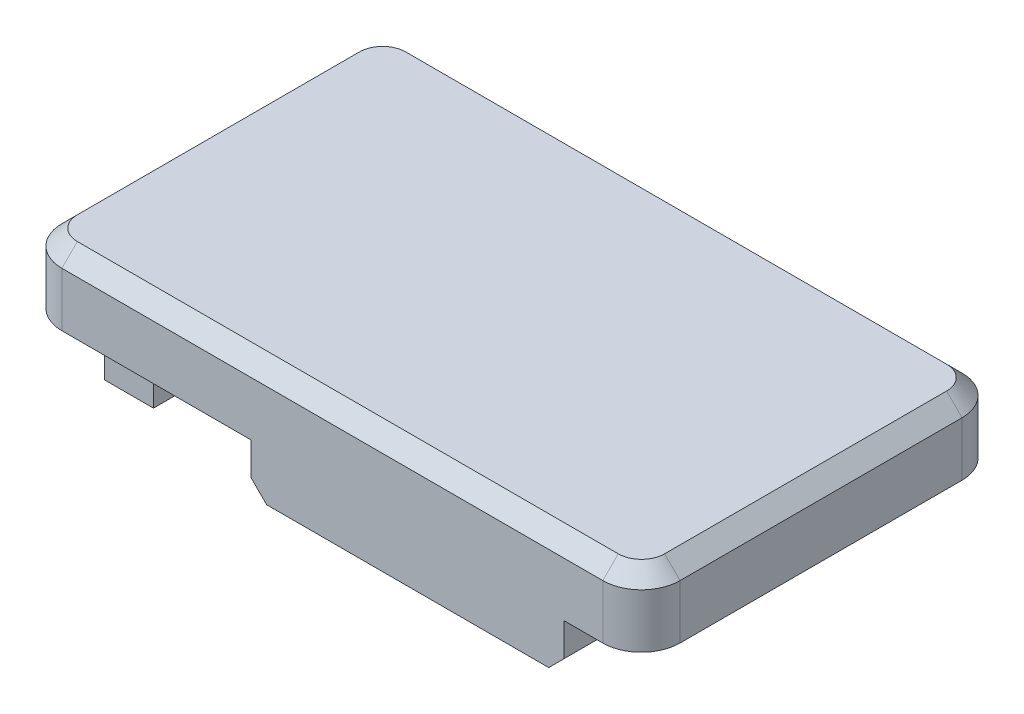
SolidWorks part; units mm, degrees
ref_plane "前视基准面" through (0, 0, 0) normal (0, 0, 1) x (1, 0, 0)
ref_plane "上视基准面" through (0, 0, 0) normal (0, 1, 0) x (1, 0, 0)
ref_plane "右视基准面" through (0, 0, 0) normal (1, 0, 0) x (0, 0, -1)
sketch "草图1" plane through (0, 0, 0) normal (0, 1, 0) x (1, 0, 0)
  line L0 (62.2995, 0) -> (94.2995, 0)
  line L1 (94.2995, 0) -> (94.2995, 18.6)
  line L2 (94.2995, 18.6) -> (62.2995, 18.6)
  line L3 (62.2995, 18.6) -> (62.2995, 0)
extrude "凸台-拉伸1" add sketch "草图1" along normal blind 3.6
sketch "草图2" plane through (0, 0, 0) normal (0, -1, 0) x (1, 0, 0)
  line L5 (64.2995, -2.2) -> (64.2995, -12.36)
  line L6 (64.2995, -12.36) -> (66.8395, -12.36)
  line L7 (66.8395, -12.36) -> (66.8395, -2.2)
  line L8 (66.8395, -2.2) -> (64.2995, -2.2)
extrude "凸台-拉伸2" add sketch "草图2" along normal blind 3.3
sketch "草图3" plane through (0, 0, 0) normal (0, -1, 0) x (1, 0, 0)
  line L1 (94.2995, -18.6) -> (62.2995, -18.6) construction
  line L2 (90.2995, -18.6) -> (74.0995, -18.6)
  line L3 (74.0995, -18.6) -> (74.0995, -16.6)
  line L4 (74.0995, -16.6) -> (90.2995, -16.6)
  line L5 (90.2995, -16.6) -> (90.2995, -18.6)
  line L7 (90.2995, -2) -> (90.2995, 0)
  line L8 (74.0995, -2) -> (90.2995, -2)
  line L9 (74.0995, 0) -> (74.0995, -2)
  line L10 (90.2995, 0) -> (74.0995, 0)
extrude "凸台-拉伸3" add sketch "草图3" along normal blind 2.5
fillet "圆角1" radius 2 4 edges at (62.2995, 1.8, -18.6) (94.2995, 1.8, -18.6) (94.2995, 1.8, 0) (62.2995, 1.8, 0)
chamfer "倒角1" distance 0.8 angle 45 8 edges at (93.7137, 3.6, -18.0142) (94.2995, 3.6, -9.3) (93.7137, 3.6, -0.5858) (78.2995, 3.6, 0) (62.8853, 3.6, -0.5858) (62.2995, 3.6, -9.3) (62.8853, 3.6, -18.0142) (78.2995, 3.6, -18.6)
chamfer "倒角2" distance 0.8 angle 45 6 edges at (74.0995, -2.5, -17.6) (90.2995, -2.5, -17.6) (82.1995, -2.5, -16.6) (74.0995, -2.5, -1) (90.2995, -2.5, -1) (82.1995, -2.5, -2)
